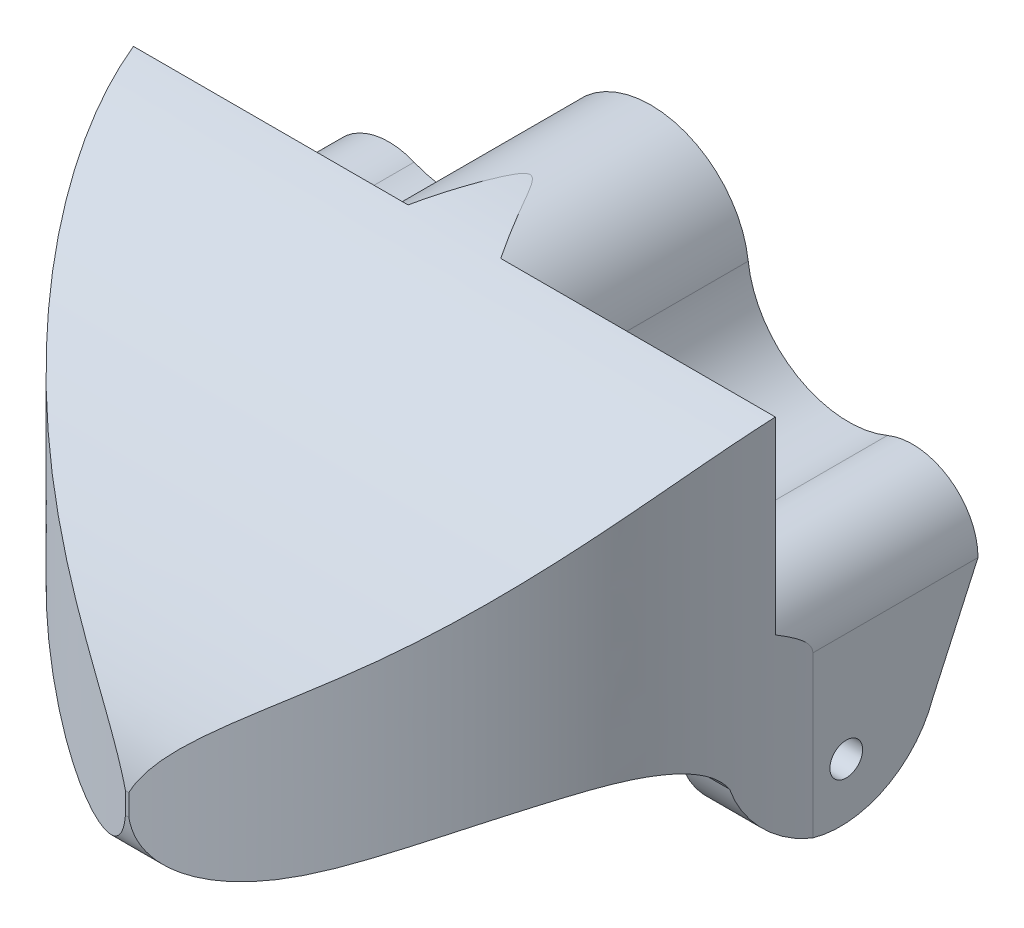
SolidWorks part; units mm, degrees
ref_plane "Front Plane" through (0, 0, 0) normal (0, 0, 1) x (1, 0, 0)
ref_plane "Top Plane" through (0, 0, 0) normal (0, 1, 0) x (1, 0, 0)
ref_plane "Right Plane" through (0, 0, 0) normal (1, 0, 0) x (0, 0, -1)
sketch "Sketch1" plane through (0, 0, 0) normal (0, 0, 1) x (1, 0, 0)
  line L1 (-25, 17.5) -> (25, 17.5)
  line L2 (-25, 17.5) -> (-25, -17.5)
  line L3 (-25, -17.5) -> (25, -17.5)
  line L4 (25, 17.5) -> (25, -17.5)
  line L5 (-25, 17.5) -> (25, -17.5) construction
  line L6 (-25, -17.5) -> (25, 17.5) construction
  point P0 (0, 0)
  dimension "D1" = 35
  dimension "D2" = 50
extrude "Boss-Extrude1" add sketch "Sketch1" along normal blind 40
sketch "Sketch3" plane through (0, 0, 0) normal (0, 0, 1) x (1, 0, 0)
  line L0 (0, 21.507) -> (0, -21.507) construction
  line L1 (-31.5636, 0) -> (31.5636, 0) construction
  line L2 (20, 0) -> (20, 18.9928) construction
  line L3 (-20, 0) -> (-20, 18.9928) construction
  line L4 (-22.5917, -4.2759) -> (-1.2958, -17.1834)
  line L5 (22.5917, -4.2759) -> (1.2958, -17.1834)
  line L7 (-25, 17.5) -> (25, 17.5)
  line L8 (-25, 17.5) -> (-25, -17.5)
  line L9 (-25, -17.5) -> (25, -17.5)
  line L10 (25, 17.5) -> (25, -17.5)
  line L11 (-25, 17.5) -> (25, -17.5) construction
  line L12 (-25, -17.5) -> (25, 17.5) construction
  circle A0 centre (0, 9.945) radius 7.5
  circle A1 centre (-20, 0) radius 5
  circle A2 centre (20, 0) radius 5
  circle A3 centre (-15.1149, 11.7465) radius 7.7219
  circle A4 centre (15.1149, 11.7465) radius 7.7219
  circle A5 centre (0, -15.0455) radius 2.5
  point P4 (0, 0)
  point P9 (0, 0)
  point P23 (0, 0)
  point P33 (-20, 0.4427)
  dimension "D1" = 15
  dimension "D3" = 10
  dimension "D4" = 5
  dimension "D2" = 20
extrude "Cut-Extrude3" cut sketch "Sketch3" along normal blind 15 contours L7 A4 A2 L10 | A4 L7 | A0 A4 L7 A3 | L7 A3 | A3 L7 L8 A1
sketch "Sketch4" plane through (0, 0, 0) normal (1, 0, 0) x (0, 0, -1)
  line L0 (-3, 31.3161) -> (-3, -19.2847) construction
  line L1 (-40, 17.5) -> (-15, 17.5) construction
  line L2 (-40, 17.5) -> (-40, -17.5) construction
  line L3 (0, 0) -> (-3.44, -7.5396)
  line L5 (0, 17.445) -> (-40, 17.445)
  line L6 (0, 17.445) -> (0, -17.5)
  line L7 (0, -17.5) -> (-40, -17.5)
  line L8 (-40, 17.445) -> (-40, -17.5)
  line L9 (6.303, 22.4395) -> (-49.0495, 22.4395)
  line L10 (6.303, 22.4395) -> (6.303, -23.1449)
  line L11 (6.303, -23.1449) -> (-49.0495, -23.1449)
  line L12 (-49.0495, 22.4395) -> (-49.0495, -23.1449)
  circle A0 centre (-10.5123, -5.0431) radius 7.5
  spline S0 degree 3 poles (-3, 17.5) (-6.4645, 17.4655) (-14.6664, 17.9152) (-24.9906, 11.7449) (-33.9623, 3.2052) (-39.2115, -3.3802) (-40, -7.9807) knots 0 0 0 0 0.217673 0.497466 0.713557 1 1 1 1
  spline S1 degree 3 poles (-17.2523, -8.3329) (-17.669, -6.1978) (-21.3826, -4.3838) (-27.8691, -5.8447) (-34.0365, -9.5313) (-40.3129, -15.4102) (-40, -7.9807) knots 0 0 0 0 0.193253 0.379939 0.648786 1 1 1 1
  point P3 (-3, 6.0157)
  dimension "D1" = 15
extrude "Cut-Extrude6" cut sketch "Sketch4" against normal through all both and the other way through all
sketch "Sketch5" plane through (0, 0, 0) normal (0, 1, 0) x (1, 0, 0)
  line L0 (0, 47.4268) -> (0, -47.4268) construction
  line L1 (-25, -15) -> (-25, -40) construction
  line L2 (-25, -12.6177) -> (-25, -40)
  line L3 (-25, -40) -> (0, -40.0512)
  line L4 (0, -40.0512) -> (25, -40)
  line L5 (25, -40) -> (25, -12.6177)
  spline S0 degree 2 poles (-25, -12.6177) (-21.8372, -31.6268) (0, -40.0512) knots 0 0 0 1 1 1
  spline S1 degree 2 poles (25, -12.6177) (21.8372, -31.6268) (0, -40.0512) knots 0 0 0 1 1 1
  point P4 (0, 0)
extrude "Cut-Extrude8" cut sketch "Sketch5" against normal through all both and the other way through all contours S0 L2 L3 | L5 S1 L4
sketch "Sketch6" plane through (0, 0, 0) normal (0, 0, 1) x (1, 0, 0)
  line L0 (-25, 0) -> (25, 0) construction
  line L1 (20, 0) -> (-20, 0)
  line L2 (20, 0) -> (20, -12.5431)
  line L3 (20, -12.5431) -> (-20, -12.5431)
  line L4 (-20, 0) -> (-20, -12.5431)
  line L5 (-25, -12.5431) -> (25, -12.5431) construction
  line L6 (-25, 21.9379) -> (-25, -21.9379) construction
  line L11 (25, 20.8074) -> (25, -20.8074) construction
  point P11 (-25, 0)
  point P13 (-25, -17.8047)
  point P16 (25, 0)
  dimension "D1" = 5
  dimension "D2" = 5
extrude "Cut-Extrude9" cut sketch "Sketch6" along normal blind 25 contours L2 L1 L4 L3
sketch "Sketch7" plane through (0, 0, 0) normal (1, 0, 0) x (0, 0, -1)
  circle A0 centre (-10.0655, -8.2979) radius 1.25
  dimension "D1" = 2.5
extrude "Cut-Extrude10" cut sketch "Sketch7" against normal through all both and the other way through all
